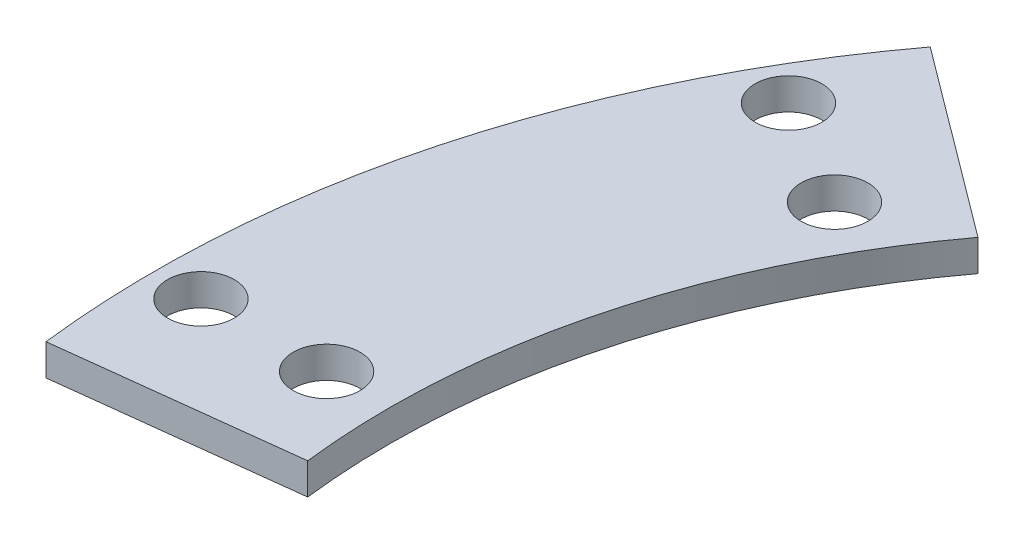
SolidWorks part; units mm, degrees
ref_plane "Front Plane" through (0, 0, 0) normal (0, 0, 1) x (1, 0, 0)
ref_plane "Top Plane" through (0, 0, 0) normal (0, 1, 0) x (1, 0, 0)
ref_plane "Right Plane" through (0, 0, 0) normal (1, 0, 0) x (0, 0, -1)
sketch "Sketch1" plane through (0, 0, 0) normal (0, 1, 0) x (1, 0, 0)
  line L0 (0, 0) -> (-59, 0) construction
  line L1 (0, 0) -> (-51.0955, 29.5) construction
  line L2 (-37.6558, 28.1254) -> (-49.6736, 37.1016)
  line L3 (-46.6736, -5.5294) -> (-61.5694, -7.2941)
  circle A0 centre (0, 0) radius 51 construction
  circle A1 centre (0, 0) radius 59 construction
  circle A2 centre (-44.1673, 25.5) radius 2.125
  circle A3 centre (-51.0955, 29.5) radius 2.125
  circle A4 centre (-59, 0) radius 2.125
  circle A5 centre (-51, 0) radius 2.125
  arc A6 (-37.6558, 28.1254) -> (-46.6736, -5.5294) centre (0, 0) ccw
  arc A7 (-49.6736, 37.1016) -> (-61.5694, -7.2941) centre (0, 0) ccw
  point P5 (-44.1673, 25.5)
  point P7 (-51, 0)
  dimension "D1" = 102
  dimension "D2" = 118
  dimension "D4" = 4.25
  dimension "D5" = 47
  dimension "D8" = 6
  dimension "D3" = 30
  dimension "D6" = 15
  dimension "D7" = 6
extrude "Boss-Extrude1" add sketch "Sketch1" along normal blind 2
